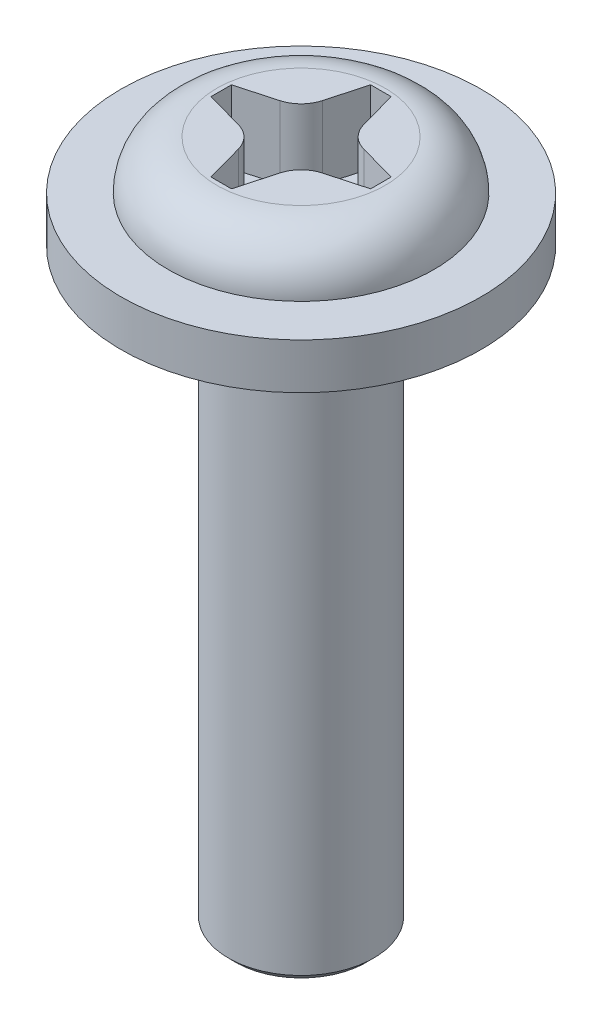
SolidWorks part; units mm, degrees
ref_plane "Front" through (0, 0, 0) normal (0, 0, 1) x (1, 0, 0)
ref_plane "Top" through (0, 0, 0) normal (0, 1, 0) x (1, 0, 0)
ref_plane "Right" through (0, 0, 0) normal (1, 0, 0) x (0, 0, -1)
sketch "Sketch1" plane through (0, 0, 0) normal (0, 0, 1) x (1, 0, 0)
  line L0 (0, 0) -> (0, -9.4) construction
  line L1 (0, -9.4) -> (0.9, -9.4)
  line L2 (0.9, -9.4) -> (1, -9.3)
  line L3 (1, -9.3) -> (1, -1.3)
  line L4 (1, -1.3) -> (2.48, -1.3)
  line L5 (2.48, -0.67) -> (1.83, -0.67)
  line L6 (1.16, 0) -> (0, 0)
  line L7 (0, 0) -> (0, -9.4)
  line L8 (2.48, -0.67) -> (2.48, -1.3)
  arc A1 (1.83, -0.67) -> (1.16, 0) centre (1.16, -0.67) ccw
  dimension "D1" = 8
  dimension "D6" = 4.96
  dimension "D2" = 2
  dimension "D3" = 0.1
  dimension "D4" = 0.1
  dimension "D5" = 1.3
  dimension "D7" = 0.63
  dimension "D8" = 3.66
revolve "Revolve1" add sketch "Sketch1" angle 360 about L0
cosmetic thread "Cosmetic Thread1" parameters "D1"=5, "D2"=1
sketch "Sketch2" plane through (0, 0, 0) normal (0, 1, 0) x (1, 0, 0)
  line L0 (0, 1.16) -> (0, 0) construction
  line L1 (0, 0) -> (1.16, 0) construction
  line L2 (0, 1.1) -> (0.1414, 1.1)
  line L3 (0.1414, 1.1) -> (0.2855, 0.5786)
  line L4 (0.3934, 0.3934) -> (0, 0) construction
  line L5 (1.1, 0.1414) -> (0.5786, 0.2855)
  line L6 (1.1, 0) -> (1.1, 0.1414)
  line L7 (0, -1.1) -> (0.1414, -1.1)
  line L8 (0.1414, -1.1) -> (0.2855, -0.5786)
  line L9 (1.1, -0.1414) -> (0.5786, -0.2855)
  line L10 (1.1, 0) -> (1.1, -0.1414)
  line L11 (-1.1, 0) -> (-1.1, -0.1414)
  line L12 (-1.1, -0.1414) -> (-0.5786, -0.2855)
  line L13 (-0.1414, -1.1) -> (-0.2855, -0.5786)
  line L14 (0, -1.1) -> (-0.1414, -1.1)
  line L15 (0, 1.1) -> (-0.1414, 1.1)
  line L16 (-0.1414, 1.1) -> (-0.2855, 0.5786)
  line L17 (-1.1, 0.1414) -> (-0.5786, 0.2855)
  line L18 (-1.1, 0) -> (-1.1, 0.1414)
  circle A0 centre (0, 0) radius 1.16 construction
  arc A1 (0.2855, 0.5786) -> (0.5786, 0.2855) centre (0.6905, 0.6905) ccw
  arc A2 (0.5786, -0.2855) -> (0.2855, -0.5786) centre (0.6905, -0.6905) ccw
  arc A3 (-0.2855, -0.5786) -> (-0.5786, -0.2855) centre (-0.6905, -0.6905) ccw
  arc A4 (-0.5786, 0.2855) -> (-0.2855, 0.5786) centre (-0.6905, 0.6905) ccw
  point P39 (0, 0)
  dimension "D1" = 45
  dimension "D2" = 2.2
  dimension "D3" = 4
extrude "Cut-Extrude1" cut sketch "Sketch2" against normal blind 1
